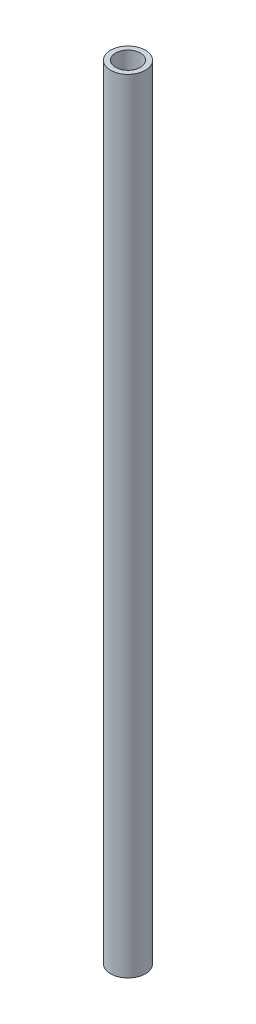
SolidWorks part; units mm, degrees
ref_plane "Front Plane" through (0, 0, 0) normal (0, 0, 1) x (1, 0, 0)
ref_plane "Top Plane" through (0, 0, 0) normal (0, 1, 0) x (1, 0, 0)
ref_plane "Right Plane" through (0, 0, 0) normal (1, 0, 0) x (0, 0, -1)
sketch "Sketch1" plane through (0, 0, 0) normal (0, 1, 0) x (1, 0, 0)
  circle A0 centre (0, 0) radius 15.875
  circle A1 centre (0, 0) radius 22.225
  dimension "D1" = 44.45
  dimension "D2" = 6.35
extrude "Boss-Extrude1" add sketch "Sketch1" along normal mid plane 1000 contours A1 A0
